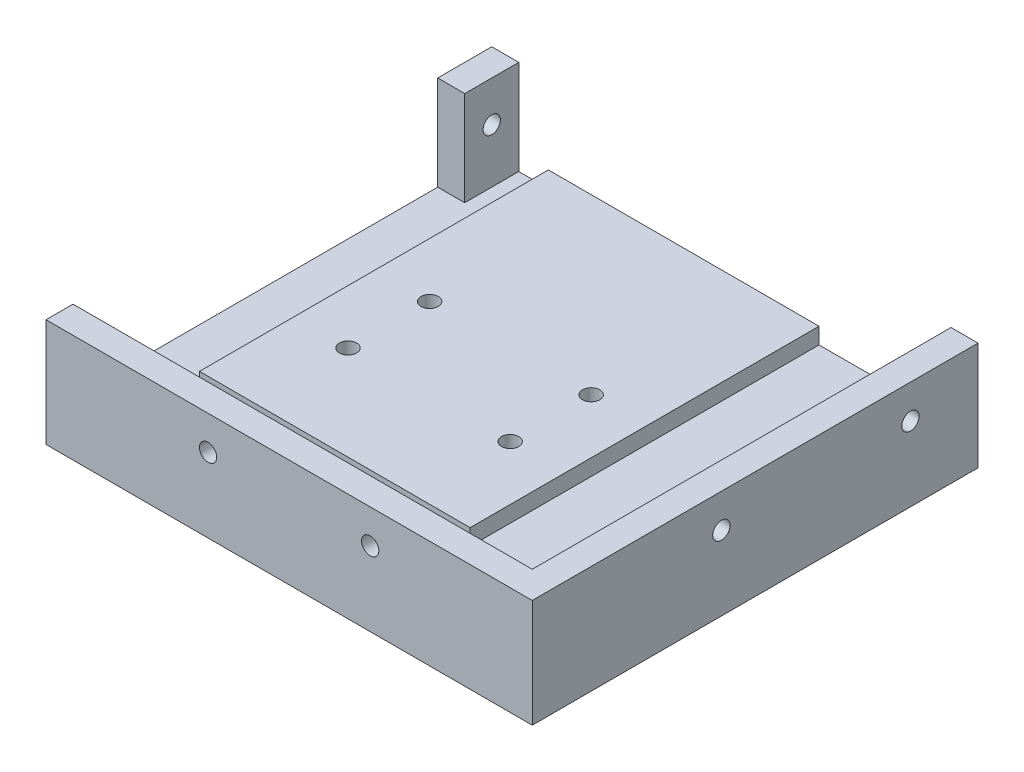
SolidWorks part; units mm, degrees
ref_plane "Front Plane" through (0, 0, 0) normal (0, 0, 1) x (1, 0, 0)
ref_plane "Top Plane" through (0, 0, 0) normal (0, 1, 0) x (1, 0, 0)
ref_plane "Right Plane" through (0, 0, 0) normal (1, 0, 0) x (0, 0, -1)
sketch "Sketch1" plane through (0, 0, 0) normal (0, 1, 0) x (1, 0, 0)
  line L1 (-45, -37.5) -> (45, -37.5)
  line L2 (-45, -37.5) -> (-45, 37.5)
  line L3 (-45, 37.5) -> (45, 37.5)
  line L4 (45, -37.5) -> (45, 37.5)
  line L5 (-45, -37.5) -> (45, 37.5) construction
  line L6 (-45, 37.5) -> (45, -37.5) construction
  point P0 (0, 0)
  dimension "D1" = 90
  dimension "D2" = 75
extrude "Boss-Extrude1" add sketch "Sketch1" along normal blind 5
sketch "Sketch2" plane through (0, 5, 0) normal (0, 1, 0) x (1, 0, 0)
  line L0 (45, -37.5) -> (45, 37.5) construction
  line L1 (-45, -37.5) -> (45, -37.5)
  line L2 (-45, -37.5) -> (-45, -32.5)
  line L3 (-45, -32.5) -> (45, -32.5)
  line L4 (45, -37.5) -> (45, -32.5)
  dimension "D1" = 5
extrude "Boss-Extrude2" add sketch "Sketch2" along normal blind 15
sketch "Sketch3" plane through (0, 0, 32.5) normal (0, 0, -1) x (-1, 0, 0)
  line L0 (-45, 5) -> (45, 5) construction
  line L1 (-45, 20) -> (-40, 20)
  line L2 (-45, 20) -> (-45, 5)
  line L3 (-45, 5) -> (-40, 5)
  line L4 (-40, 20) -> (-40, 5)
  dimension "D1" = 5
extrude "Boss-Extrude3" add sketch "Sketch3" along normal up to surface (70 mm away) up to face at (0, 2.5, -37.5)
sketch "Sketch5" plane through (45, 0, 0) normal (1, 0, 0) x (0, 0, -1)
  circle A0 centre (-2.5, 13.75) radius 1.6
  circle A1 centre (32.5, 13.75) radius 1.6
extrude "Cut-Extrude1" cut sketch "Sketch5" against normal up to next
sketch "Sketch7" plane through (0, 0, 37.5) normal (0, 0, 1) x (1, 0, 0)
  circle A0 centre (-15, 13.75) radius 1.6
  circle A1 centre (15, 13.75) radius 1.6
extrude "Cut-Extrude3" cut sketch "Sketch7" against normal up to next
sketch "Sketch8" plane through (0, 5, 0) normal (0, 1, 0) x (1, 0, 0)
  line L0 (40, 37.5) -> (-45, 37.5) construction
  line L1 (15.5808, 37.5) -> (-34.5192, 37.5)
  line L2 (15.5808, 37.5) -> (15.5808, -19.5793)
  line L3 (15.5808, -19.5793) -> (-34.5192, -19.5793)
  line L4 (-34.5192, 37.5) -> (-34.5192, -19.5793)
  line L5 (15.5808, -7.8293) -> (15.5808, 42.1707) construction
extrude "Boss-Extrude6" add sketch "Sketch8" along normal blind 3
sketch "Sketch9" plane through (0, 8, 0) normal (0, 1, 0) x (1, 0, 0)
  line L0 (5.4808, 20.4207) -> (5.4808, 12.9207) construction
  line L2 (5.4808, -9.5793) -> (5.4808, -2.0793) construction
  line L3 (-24.5192, -9.5793) -> (-24.5192, -2.0793) construction
  line L5 (-24.5192, 20.4207) -> (-24.4192, 12.9207) construction
  line L6 (-24.4192, 1.1707) -> (-24.4192, 42.1707) construction
  circle A2 centre (-24.4192, 12.9207) radius 1.6
  circle A4 centre (5.4808, 12.9207) radius 1.6
  circle A5 centre (5.4808, -2.0793) radius 1.6
  circle A6 centre (-24.5192, -2.0793) radius 1.6
  dimension "D5" = 3.2
  dimension "D6" = 3.2
  dimension "D7" = 3.2
  dimension "D8" = 3.2
  dimension "D1" = 7.5
  dimension "D2" = 7.5
  dimension "D3" = 7.5
  dimension "D4" = 7.5
extrude "Cut-Extrude4" cut sketch "Sketch9" against normal up to next
sketch "Sketch10" plane through (0, 8, 0) normal (0, 1, 0) x (1, 0, 0)
  line L1 (-21.0914, -2.3042) -> (-22.6105, 0.7769)
  line L2 (-22.6105, 0.7769) -> (-26.0383, 1.0018)
  line L3 (-26.0383, 1.0018) -> (-27.9471, -1.8543)
  line L4 (-27.9471, -1.8543) -> (-26.428, -4.9354)
  line L5 (-26.428, -4.9354) -> (-23.0001, -5.1604)
  line L6 (-23.0001, -5.1604) -> (-21.0914, -2.3042)
  line L7 (8.9086, -2.3042) -> (7.3895, 0.7769)
  line L8 (7.3895, 0.7769) -> (3.9617, 1.0018)
  line L9 (3.9617, 1.0018) -> (2.0529, -1.8543)
  line L10 (2.0529, -1.8543) -> (3.572, -4.9354)
  line L11 (3.572, -4.9354) -> (6.9999, -5.1604)
  line L12 (6.9999, -5.1604) -> (8.9086, -2.3042)
  line L13 (8.9086, 12.6958) -> (7.3895, 15.7769)
  line L14 (7.3895, 15.7769) -> (3.9617, 16.0018)
  line L15 (3.9617, 16.0018) -> (2.0529, 13.1457)
  line L16 (2.0529, 13.1457) -> (3.572, 10.0646)
  line L17 (3.572, 10.0646) -> (6.9999, 9.8396)
  line L18 (6.9999, 9.8396) -> (8.9086, 12.6958)
  line L19 (-20.9914, 12.6958) -> (-22.5105, 15.7769)
  line L20 (-22.5105, 15.7769) -> (-25.9383, 16.0018)
  line L21 (-25.9383, 16.0018) -> (-27.8471, 13.1457)
  line L22 (-27.8471, 13.1457) -> (-26.328, 10.0646)
  line L23 (-26.328, 10.0646) -> (-22.9001, 9.8396)
  line L24 (-22.9001, 9.8396) -> (-20.9914, 12.6958)
  circle A0 centre (-24.5192, -2.0793) radius 2.975 construction
  circle A1 centre (5.4808, -2.0793) radius 2.975 construction
  circle A2 centre (5.4808, 12.9207) radius 2.975 construction
  circle A3 centre (-24.4192, 12.9207) radius 2.975 construction
  dimension "D1" = 5.95
  dimension "D2" = 5.95
  dimension "D3" = 5.95
  dimension "D4" = 5.95
extrude "Cut-Extrude5" cut sketch "Sketch10" against normal blind 2.5 from offset 2.5 offset against normal yes
sketch "Sketch11" plane through (0, 0, -37.5) normal (0, 0, -1) x (-1, 0, 0)
  line L0 (-45, 20) -> (-45, 0)
  line L1 (-45, 0) -> (45, 0)
  line L2 (-45, 0) -> (45, 0) construction
  line L3 (45, 0) -> (45, 5)
  line L4 (45, 5) -> (34.5192, 5)
  line L5 (34.5192, 5) -> (34.5192, 8)
  line L6 (34.5192, 8) -> (-15.5808, 8)
  line L7 (-15.5808, 8) -> (-15.5808, 5)
  line L8 (-15.5808, 8) -> (-15.5808, 5) construction
  line L9 (-40, 5) -> (45, 5) construction
  line L10 (-15.5808, 5) -> (-40, 5)
  line L11 (-40, 5) -> (-40, 20)
  line L12 (-40, 20) -> (-45, 20)
extrude "Boss-Extrude7" add sketch "Sketch11" along normal blind 7.5
sketch "Sketch12" plane through (0, 5, 0) normal (0, 1, 0) x (1, 0, 0)
  line L1 (-45, 45) -> (-40, 45)
  line L2 (-45, 45) -> (-45, 35)
  line L3 (-45, 35) -> (-40, 35)
  line L4 (-40, 45) -> (-40, 35)
  dimension "D1" = 5
  dimension "D2" = 10
extrude "Boss-Extrude8" add sketch "Sketch12" along normal blind 17.5
sketch "Sketch13" plane through (-45, 0, 0) normal (-1, 0, 0) x (0, 0, 1)
  circle A0 centre (-40, 15) radius 1.6
extrude "Cut-Extrude6" cut sketch "Sketch13" against normal up to next
